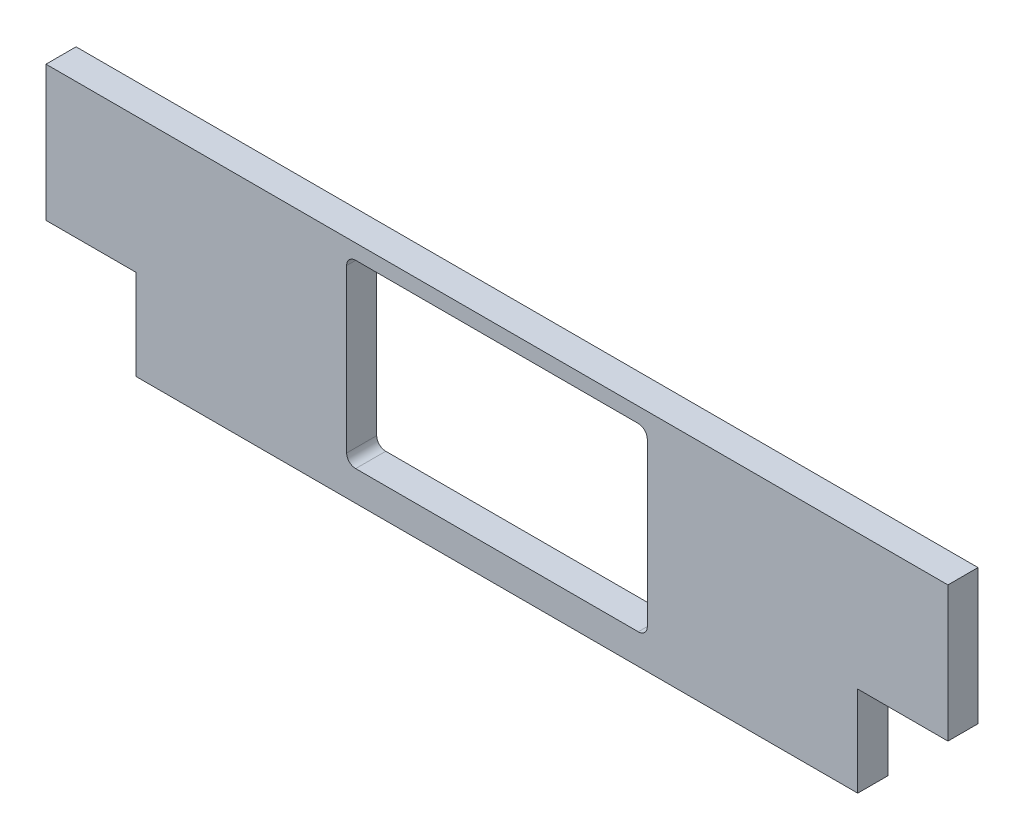
SolidWorks part; units mm, degrees
ref_plane "Ebene vorne" through (0, 0, 0) normal (0, 0, 1) x (1, 0, 0)
ref_plane "Ebene oben" through (0, 0, 0) normal (0, 1, 0) x (1, 0, 0)
ref_plane "Ebene rechts" through (0, 0, 0) normal (1, 0, 0) x (0, 0, -1)
sketch "Skizze1" plane through (0, 0, 0) normal (0, 0, 1) x (1, 0, 0)
  line L0 (-150, -75) -> (-150, 55) construction
  line L1 (150, -150) -> (-150, -150)
  line L2 (150, -150) -> (150, -75)
  line L3 (150, -75) -> (-150, -75)
  line L4 (-150, -150) -> (-150, -75)
  dimension "D1" = 75
extrude "Linear austragen1" add sketch "Skizze1" along normal blind 10
sketch "Skizze2" plane through (0, 0, 10) normal (0, 0, 1) x (1, 0, 0)
  line L0 (-150, -150) -> (150, -150) construction
  line L1 (50, -140) -> (-50, -140)
  line L2 (50, -140) -> (50, -80)
  line L3 (50, -80) -> (-50, -80)
  line L4 (-50, -140) -> (-50, -80)
  line L5 (50, -140) -> (150, -140) construction
  line L7 (-50, -140) -> (-150, -140) construction
  line L8 (-150, 55) -> (-150, -150) construction
  line L9 (150, -150) -> (150, -75) construction
  dimension "D1" = 10
  dimension "D2" = 100
  dimension "D3" = 60
extrude "Schnitt-Linear austragen1" cut sketch "Skizze2" against normal blind 10
fillet "Verrundung1" radius 3 4 edges at (-50, -140, 5) (50, -140, 5) (-50, -80, 5) (50, -80, 5)
sketch "Skizze4" plane through (150, 0, 0) normal (1, 0, 0) x (0, 0, -1)
  line L0 (0, -120) -> (-10, -120)
  line L1 (0, -150) -> (0, -75) construction
  line L2 (-10, -150) -> (-10, -75) construction
  line L3 (-10, -120) -> (-10, -150)
  line L4 (-10, -150) -> (0, -150)
  line L5 (0, -150) -> (0, -120)
  dimension "D1" = 30
extrude "Schnitt-Linear austragen2" cut sketch "Skizze4" against normal blind 30
mirror "Spiegeln1" about plane through (0, 0, 0) normal (1, 0, 0) of "Schnitt-Linear austragen2"
